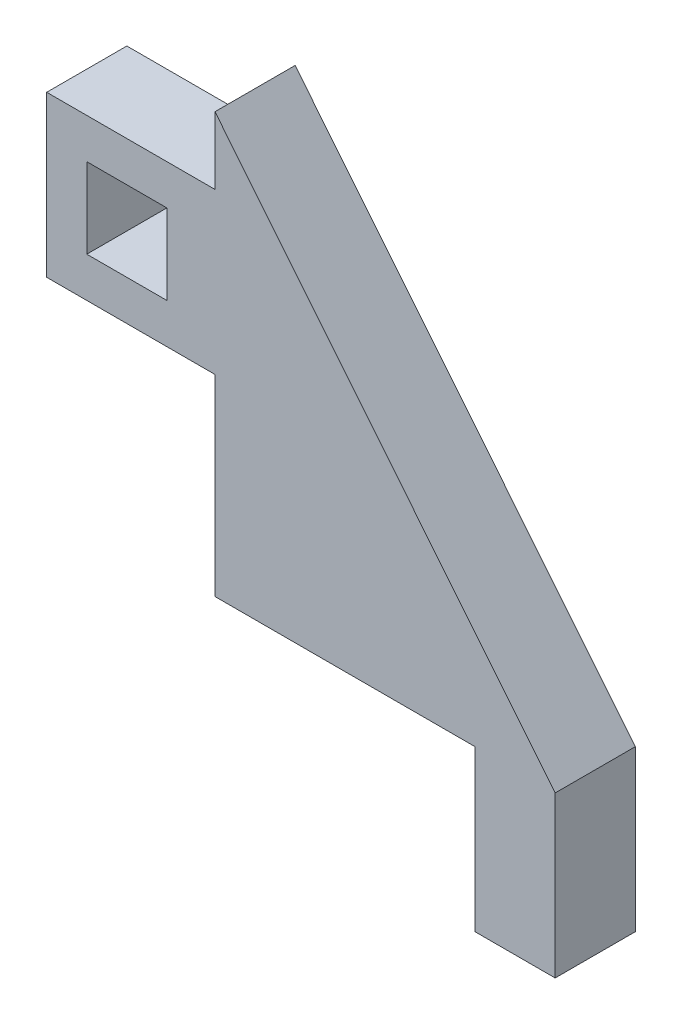
SolidWorks part; units mm, degrees
ref_plane "Plan de face" through (0, 0, 0) normal (0, 0, 1) x (1, 0, 0)
ref_plane "Plan de dessus" through (0, 0, 0) normal (0, 1, 0) x (1, 0, 0)
ref_plane "Plan de droite" through (0, 0, 0) normal (1, 0, 0) x (0, 0, -1)
sketch "Esquisse1" plane through (0, 0, 0) normal (0, 0, 1) x (1, 0, 0)
  line L0 (0, 0) -> (0, 26.2)
  line L1 (0, 26.2) -> (21.2264, 0)
  line L2 (21.2264, 0) -> (0, 0)
  dimension "D1" = 21.2264
  dimension "D2" = 26.2
extrude "Boss.-Extru.1" add sketch "Esquisse1" along normal blind 5
sketch "Esquisse2" plane through (0, 0, 0) normal (-1, 0, 0) x (0, 0, 1)
  line L0 (0, 26.2) -> (0, 0) construction
  line L1 (0, 12) -> (5, 12)
  line L2 (0, 12) -> (0, 22)
  line L3 (5, 0) -> (0, 0) construction
  line L6 (0, 22) -> (5, 22)
  line L7 (5, 22) -> (5, 12)
  dimension "D1" = 10
  dimension "D2" = 12
sketch "Esquisse3" plane through (0, 0, 0) normal (0, -1, 0) x (1, 0, 0)
  line L0 (0, 0) -> (21.2264, 0) construction
  line L1 (21.2264, 5) -> (16.2264, 5)
  line L2 (21.2264, 5) -> (21.2264, 0)
  line L3 (21.2264, 0) -> (16.2264, 0)
  line L4 (16.2264, 5) -> (16.2264, 0)
  dimension "D1" = 5
extrude "Boss.-Extru.3" add sketch "Esquisse3" along normal blind 10
extrude "Boss.-Extru.5" add sketch "Esquisse2" along normal blind 10.5
sketch "Esquisse4" plane through (0, 0, 0) normal (0, 0, -1) x (-1, 0, 0)
  line L0 (0, 26.2) -> (0, 22) construction
  line L1 (3, 19.5) -> (8, 19.5)
  line L2 (3, 19.5) -> (3, 14.5)
  line L3 (3, 14.5) -> (8, 14.5)
  line L4 (8, 19.5) -> (8, 14.5)
  line L5 (10.5, 12) -> (0, 12) construction
  dimension "D1" = 5
  dimension "D2" = 5
  dimension "D3" = 3
  dimension "D4" = 2.5
extrude "Enlèv. mat.-Extru.1" cut sketch "Esquisse4" against normal blind 10
